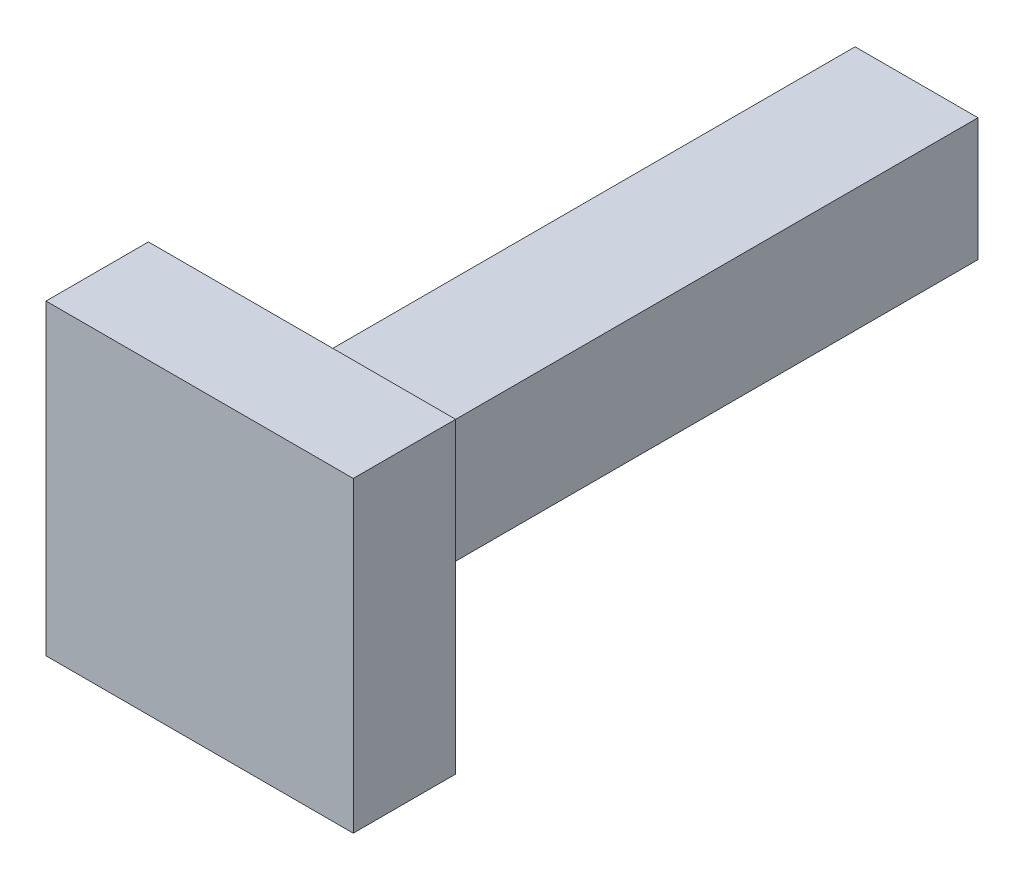
SolidWorks part; units mm, degrees
ref_plane "Front Plane" through (0, 0, 0) normal (0, 0, 1) x (1, 0, 0)
ref_plane "Top Plane" through (0, 0, 0) normal (0, 1, 0) x (1, 0, 0)
ref_plane "Right Plane" through (0, 0, 0) normal (1, 0, 0) x (0, 0, -1)
sketch "Sketch1" plane through (0, 0, 0) normal (0, 0, 1) x (1, 0, 0)
  line L1 (0, 0) -> (12, 0)
  line L2 (0, 0) -> (0, 12)
  line L3 (0, 12) -> (12, 12)
  line L4 (12, 0) -> (12, 12)
  dimension "D1" = 12
  dimension "D2" = 12
extrude "Boss-Extrude1" add sketch "Sketch1" along normal blind 60
sketch "Sketch2" plane through (0, 0, 60) normal (0, 0, 1) x (1, 0, 0)
  line L0 (12, 12) -> (0, 12) construction
  line L1 (21, -9) -> (-9, -9)
  line L2 (21, -9) -> (21, 21)
  line L3 (21, 21) -> (-9, 21)
  line L4 (-9, -9) -> (-9, 21)
  line L5 (21, -9) -> (-9, 21) construction
  line L6 (21, 21) -> (-9, -9) construction
  line L7 (12, 0) -> (12, 12) construction
  point P0 (6, 6)
  point P9 (6, 12)
  point P12 (12, 6)
  dimension "D1" = 30
  dimension "D2" = 30
extrude "Boss-Extrude2" add sketch "Sketch2" along normal blind 10
